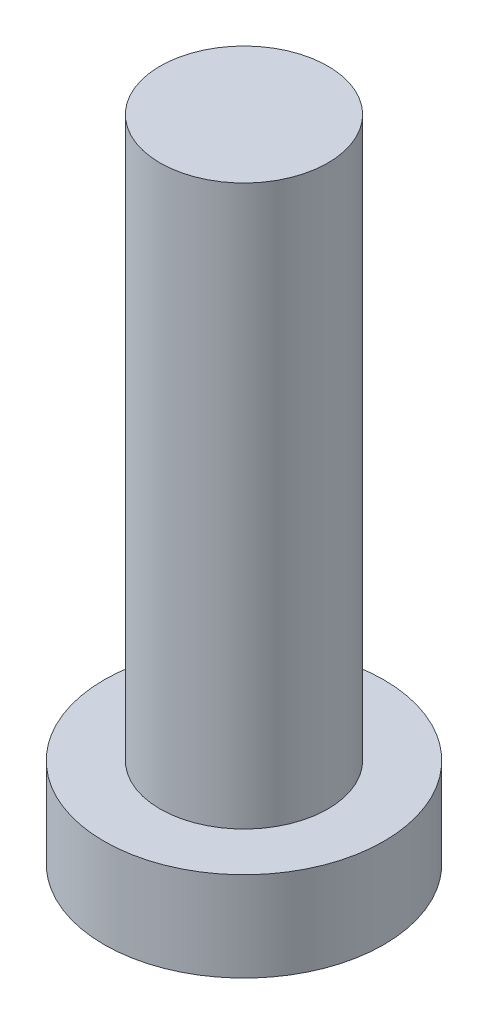
SolidWorks part; units mm, degrees
ref_plane "前视基准面" through (0, 0, 0) normal (0, 0, 1) x (1, 0, 0)
ref_plane "上视基准面" through (0, 0, 0) normal (0, 1, 0) x (1, 0, 0)
ref_plane "右视基准面" through (0, 0, 0) normal (1, 0, 0) x (0, 0, -1)
sketch "草图1" plane through (0, 0, 0) normal (0, 1, 0) x (1, 0, 0)
  circle A0 centre (0, 0) radius 2.5
extrude "凸台-拉伸1" add sketch "草图1" along normal blind 1.6
sketch "草图2" plane through (0, 1.6, 0) normal (0, 1, 0) x (1, 0, 0)
  circle A0 centre (0, 0) radius 1.5
extrude "凸台-拉伸2" add sketch "草图2" along normal blind 10
sketch "草图3" plane through (0, 0, 0) normal (0, -1, 0) x (1, 0, 0)
  line L0 (-0.5, 1) -> (-0.5, 1.75)
  line L1 (-1.75, -0.5) -> (-1, -0.5)
  line L2 (-1.75, -0.5) -> (-1.75, 0.5)
  line L3 (-1.75, 0.5) -> (-1, 0.5)
  line L4 (1.75, -0.5) -> (1.75, 0.5)
  line L5 (-1.75, -0.5) -> (1.75, 0.5) construction
  line L6 (-1.75, 0.5) -> (1.75, -0.5) construction
  line L7 (-0.5, -1.75) -> (0.5, -1.75)
  line L8 (-0.5, -1.75) -> (-0.5, -1)
  line L9 (-0.5, 1.75) -> (0.5, 1.75)
  line L10 (0.5, -1.75) -> (0.5, -1)
  line L11 (-0.5, -1.75) -> (0.5, 1.75) construction
  line L12 (-0.5, 1.75) -> (0.5, -1.75) construction
  line L13 (1, -0.5) -> (1.75, -0.5)
  line L14 (0.5, 1) -> (0.5, 1.75)
  line L15 (1, 0.5) -> (1.75, 0.5)
  arc A0 (1, -0.5) -> (0.5, -1) centre (1, -1) ccw
  arc A1 (-0.5, -1) -> (-1, -0.5) centre (-1, -1) ccw
  arc A2 (0.5, 1) -> (1, 0.5) centre (1, 1) ccw
  arc A3 (-0.5, 1) -> (-1, 0.5) centre (-1, 1) cw
  point P0 (0, 0)
  point P6 (0, 0)
  point P21 (0.5, 0.5)
  dimension "D1" = 0.5
extrude "切除-拉伸1" cut sketch "草图3" against normal blind 1
